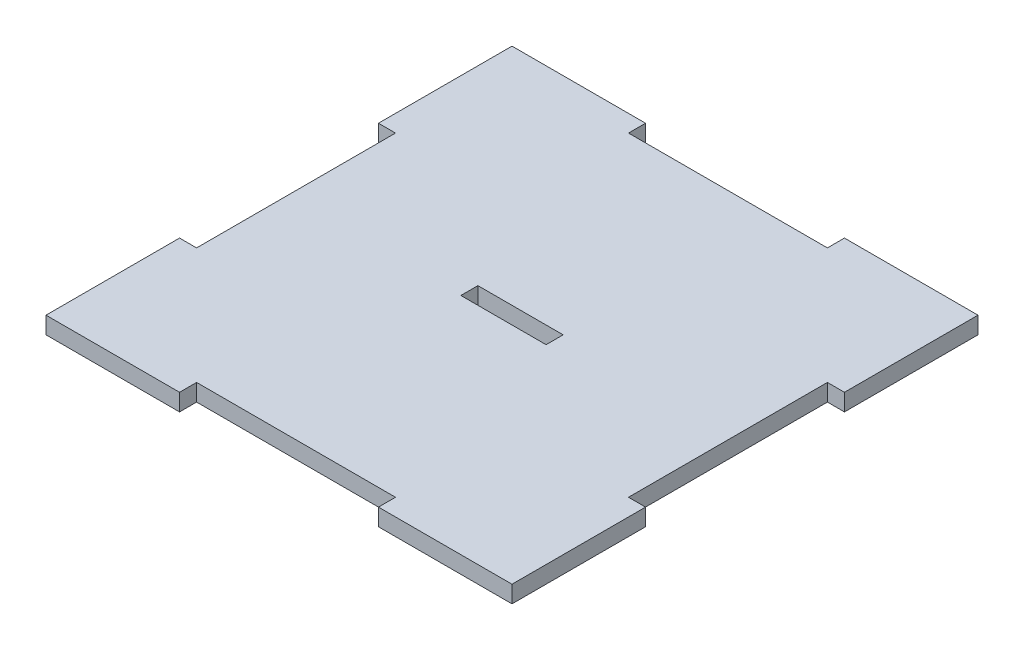
SolidWorks part; units mm, degrees
ref_plane "Front Plane" through (0, 0, 0) normal (0, 0, 1) x (1, 0, 0)
ref_plane "Top Plane" through (0, 0, 0) normal (0, 1, 0) x (1, 0, 0)
ref_plane "Right Plane" through (0, 0, 0) normal (1, 0, 0) x (0, 0, -1)
sketch "Sketch1" plane through (0, 0, 0) normal (0, 1, 0) x (1, 0, 0)
  line L0 (0, 38) -> (0, -38) construction
  line L1 (-41, -41) -> (-17.5, -41)
  line L2 (-41, -41) -> (-41, -17.5)
  line L3 (-41, 41) -> (-17.5, 41)
  line L4 (41, -41) -> (41, -17.5)
  line L5 (-41, -41) -> (41, 41) construction
  line L6 (-41, 41) -> (41, -41) construction
  line L11 (-41, 17.5) -> (-38, 17.5)
  line L12 (-38, 17.5) -> (-38, -17.5)
  line L13 (-35, 0) -> (38, 0) construction
  line L26 (17.5, 41) -> (41, 41)
  line L27 (41, 17.5) -> (41, 41)
  line L28 (17.5, -41) -> (41, -41)
  line L29 (-41, 17.5) -> (-41, 41)
  line L30 (-38, -17.5) -> (-41, -17.5)
  line L31 (-17.5, 41) -> (-17.5, 38)
  line L32 (-17.5, 38) -> (17.5, 38)
  line L33 (17.5, 38) -> (17.5, 41)
  line L34 (41, 17.5) -> (38, 17.5)
  line L35 (38, 17.5) -> (38, -17.5)
  line L36 (38, -17.5) -> (41, -17.5)
  line L37 (17.5, -41) -> (17.5, -38)
  line L38 (17.5, -38) -> (-17.5, -38)
  line L39 (-17.5, -38) -> (-17.5, -41)
  point P0 (0, 0)
  point P6 (0, 0)
  dimension "D1" = 3
  dimension "D2" = 82
  dimension "D3" = 3
  dimension "D4" = 82
  dimension "D5" = 3
  dimension "D6" = 3
extrude "Boss-Extrude1" add sketch "Sketch1" along normal blind 3
sketch "Sketch2" plane through (0, 3, 0) normal (0, 1, 0) x (1, 0, 0)
  line L9 (-7.5, 1.5) -> (7.5, 1.5)
  line L10 (-7.5, 1.5) -> (-7.5, -1.5)
  line L11 (-7.5, -1.5) -> (7.5, -1.5)
  line L12 (7.5, 1.5) -> (7.5, -1.5)
  line L13 (-7.5, 1.5) -> (7.5, -1.5) construction
  line L14 (-7.5, -1.5) -> (7.5, 1.5) construction
  point P0 (0, 0)
  dimension "D1" = 15
  dimension "D2" = 3
extrude "Cut-Extrude1" cut sketch "Sketch2" against normal blind 3
